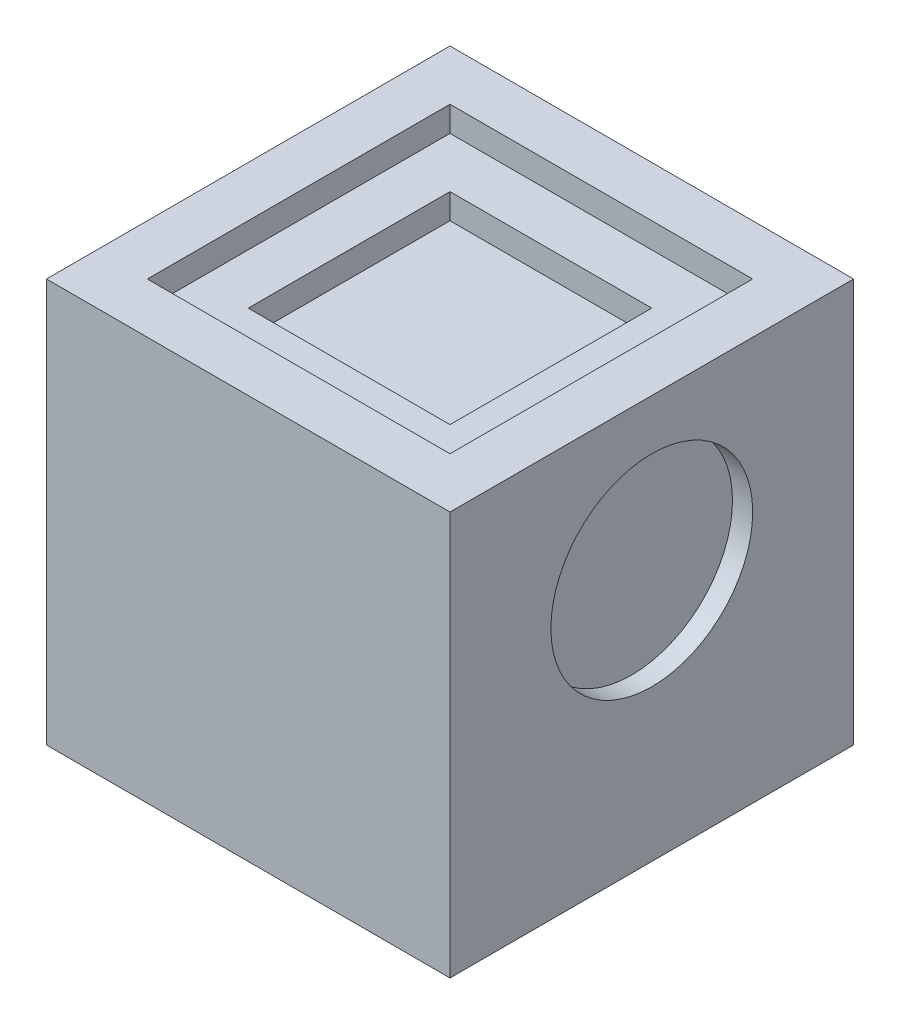
SolidWorks part; units mm, degrees
ref_plane "Front Plane" through (0, 0, 0) normal (0, 0, 1) x (1, 0, 0)
ref_plane "Top Plane" through (0, 0, 0) normal (0, 1, 0) x (1, 0, 0)
ref_plane "Right Plane" through (0, 0, 0) normal (1, 0, 0) x (0, 0, -1)
sketch "Sketch1" plane through (0, 0, 0) normal (0, 1, 0) x (1, 0, 0)
  line L1 (-25.4, -25.4) -> (25.4, -25.4)
  line L2 (-25.4, -25.4) -> (-25.4, 25.4)
  line L3 (-25.4, 25.4) -> (25.4, 25.4)
  line L4 (25.4, -25.4) -> (25.4, 25.4)
  line L5 (-25.4, -25.4) -> (25.4, 25.4) construction
  line L6 (-25.4, 25.4) -> (25.4, -25.4) construction
  point P0 (0, 0)
  dimension "D1" = 50.8
  dimension "D2" = 50.8
extrude "Boss-Extrude1" add sketch "Sketch1" along normal blind 50.8
sketch "Sketch4" plane through (25.4, 0, 0) normal (1, 0, 0) x (0, 0, -1)
  circle A0 centre (0, 31.75) radius 12.7
  dimension "D1" = 25.4
extrude "Cut-Extrude3" cut sketch "Sketch4" against normal blind 2.54
sketch "Sketch5" plane through (0, 50.8, 0) normal (0, 1, 0) x (1, 0, 0)
  line L1 (-19.05, -19.05) -> (19.05, -19.05)
  line L2 (-19.05, -19.05) -> (-19.05, 19.05)
  line L3 (-19.05, 19.05) -> (19.05, 19.05)
  line L4 (19.05, -19.05) -> (19.05, 19.05)
  line L5 (-19.05, -19.05) -> (19.05, 19.05) construction
  line L6 (-19.05, 19.05) -> (19.05, -19.05) construction
  point P0 (0, 0)
  dimension "D1" = 38.1
  dimension "D2" = 38.1
extrude "Cut-Extrude5" cut sketch "Sketch5" against normal blind 3.175
sketch "Sketch6" plane through (0, 47.625, 0) normal (0, 1, 0) x (1, 0, 0)
  line L1 (-12.7, -12.7) -> (12.7, -12.7)
  line L2 (-12.7, -12.7) -> (-12.7, 12.7)
  line L3 (-12.7, 12.7) -> (12.7, 12.7)
  line L4 (12.7, -12.7) -> (12.7, 12.7)
  line L5 (-12.7, -12.7) -> (12.7, 12.7) construction
  line L6 (-12.7, 12.7) -> (12.7, -12.7) construction
  point P1 (0, 0)
  dimension "D1" = 25.4
  dimension "D2" = 25.4
extrude "Cut-Extrude6" cut sketch "Sketch6" against normal blind 3.175
